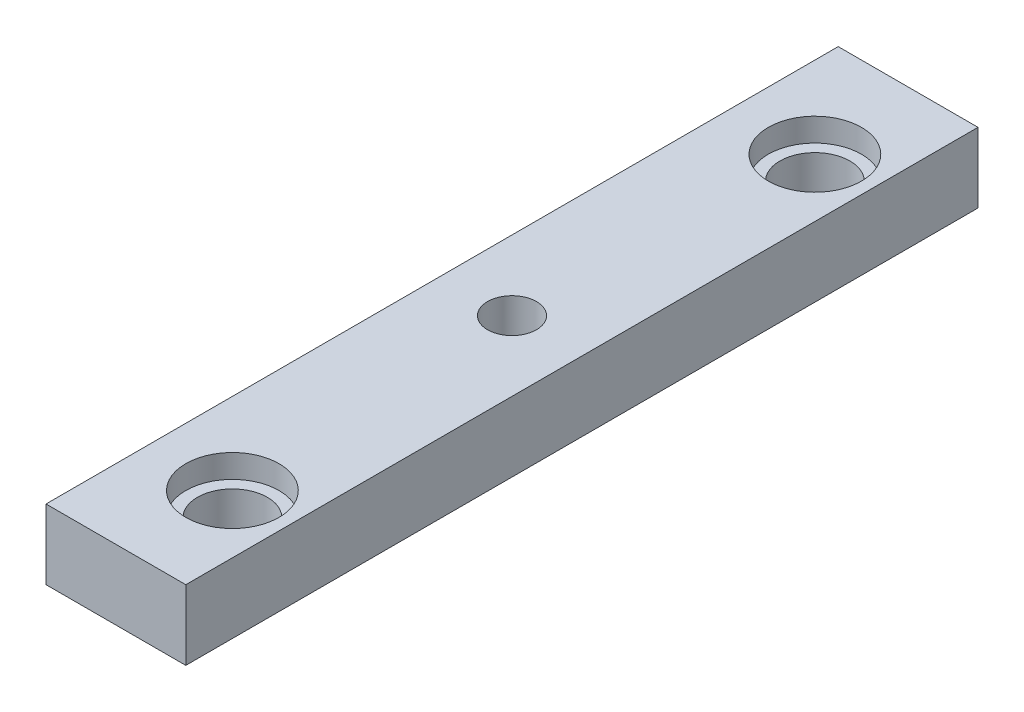
SolidWorks part; units mm, degrees
ref_plane "Front" through (0, 0, 0) normal (0, 0, 1) x (1, 0, 0)
ref_plane "Top" through (0, 0, 0) normal (0, 1, 0) x (1, 0, 0)
ref_plane "Right" through (0, 0, 0) normal (1, 0, 0) x (0, 0, -1)
sketch "Sketch1" plane through (0, 0, 0) normal (0, 0, 1) x (1, 0, 0)
  line L1 (6, 3) -> (-6, 3)
  line L2 (6, 3) -> (6, -3)
  line L3 (6, -3) -> (-6, -3)
  line L4 (-6, 3) -> (-6, -3)
  point P4 (6, 0)
  point P6 (0, 3)
  dimension "D1" = 12
  dimension "D2" = 6
extrude "Boss-Extrude1" add sketch "Sketch1" along normal blind 60
sketch "Sketch2" plane through (0, 3, 0) normal (0, 1, 0) x (1, 0, 0)
  line L0 (6, -60) -> (6, 0) construction
  line L1 (6, 0) -> (-6, 0) construction
  circle A0 centre (1, -5) radius 3
  circle A1 centre (1, -55) radius 3
  dimension "D1" = 6
  dimension "D2" = 5
  dimension "D3" = 5
  dimension "D4" = 50
extrude "Cut-Extrude1" cut sketch "Sketch2" against normal through all
sketch "Sketch3" plane through (0, 3, 0) normal (0, 1, 0) x (1, 0, 0)
  circle A0 centre (1, -5) radius 4
  circle A1 centre (1, -55) radius 4
  dimension "D1" = 8
extrude "Cut-Extrude2" cut sketch "Sketch3" against normal blind 2
sketch "Sketch4" plane through (0, 0, 0) normal (0, 0, -1) x (-1, 0, 0)
  line L0 (-6, 3) -> (6, 3) construction
  line L1 (6, 3) -> (-6, 3)
  line L2 (6, 3) -> (6, -3)
  line L3 (6, -3) -> (-6, -3)
  line L4 (-6, 3) -> (-6, -3)
  line L5 (6, -3) -> (-6, -3) construction
  line L6 (-6, -3) -> (-6, 3) construction
  line L7 (6, 3) -> (6, -3) construction
extrude "Boss-Extrude2" add sketch "Sketch4" along normal blind 4
sketch "Sketch5" plane through (0, 0, 60) normal (0, 0, 1) x (1, 0, 0)
  line L0 (6, 3) -> (-6, 3) construction
  line L1 (6, 3) -> (-6, 3)
  line L2 (6, 3) -> (6, -3)
  line L3 (6, -3) -> (-6, -3)
  line L4 (-6, 3) -> (-6, -3)
  line L5 (-6, -3) -> (6, -3) construction
  line L6 (-6, 3) -> (-6, -3) construction
  line L7 (6, -3) -> (6, 3) construction
extrude "Boss-Extrude3" add sketch "Sketch5" along normal blind 4
hole_wizard "M5 Tapped Hole1" positions "Sketch7" profile "Sketch6" tap size "M5" standard "ISO"
sketch "Sketch7" plane through (0, 3, 0) normal (0, 1, 0) x (-1, 0, 0)
  line L0 (-6, 64) -> (-6, -4) construction
  line L3 (-6, 30) -> (6, 30) construction
  line L5 (-6, 64) -> (6, 64) construction
  line L6 (6, -4) -> (-6, -4) construction
  line L7 (6, 64) -> (6, -4) construction
  point P0 (0, 30)
  dimension "D1" = 6
sketch "Sketch6" plane through (0, 3, 30) normal (1, 0, 0) x (0, 0, 1)
  line L0 (0, 0) -> (0, 53.2618)
  line L1 (0, 53.2618) -> (2.1, 52)
  line L2 (2.1, 52) -> (2.1, 0)
  line L5 (2.1, 0) -> (0, 0)
  line L10 (0, 53.2618) -> (-2.1, 52) construction
  line L11 (0, -6.35) -> (0, 107.95) construction
  dimension "Tap Drill Dia." = 4.2
  dimension "Tap Drill Depth" = 52
  dimension "Drill Angle" = 118
cosmetic thread "Hole Thread1" parameters "D1"=6, "D2"=5
